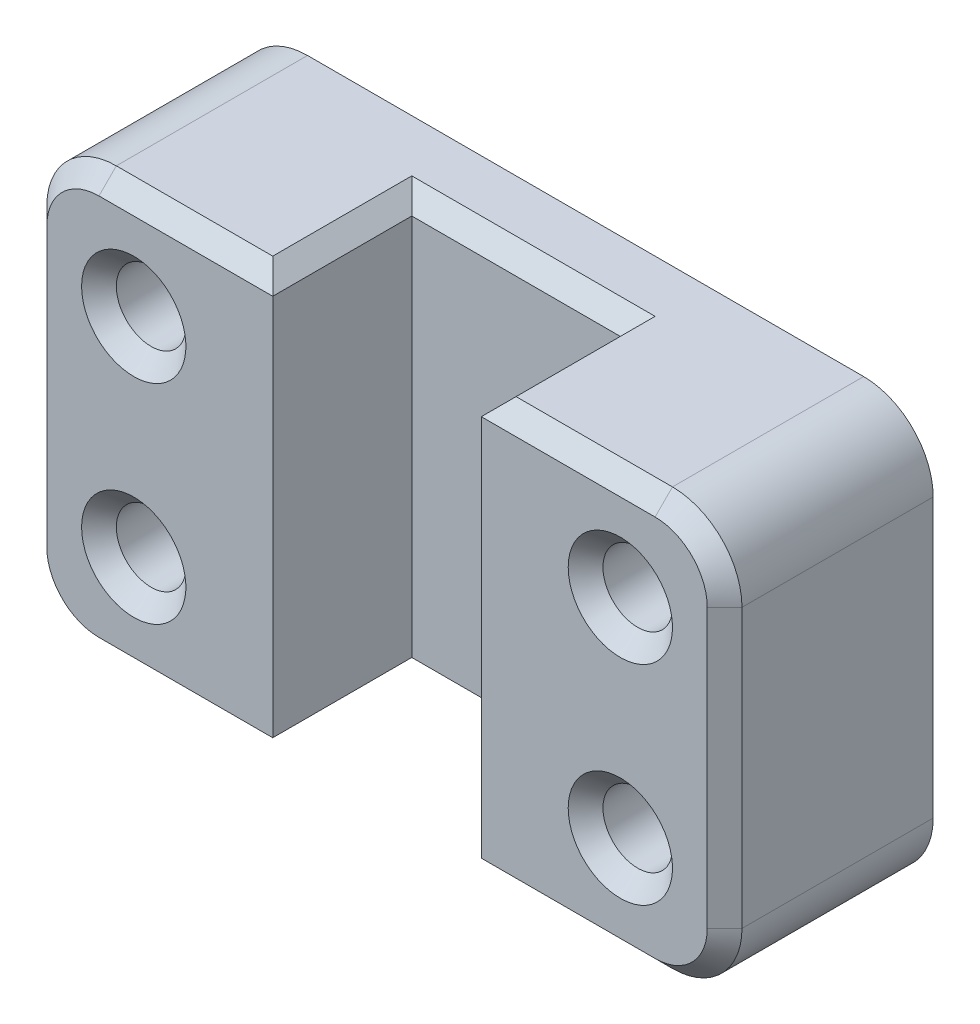
SolidWorks part; units mm, degrees
ref_plane "Front Plane" through (0, 0, 0) normal (0, 0, 1) x (1, 0, 0)
ref_plane "Top Plane" through (0, 0, 0) normal (0, 1, 0) x (1, 0, 0)
ref_plane "Right Plane" through (0, 0, 0) normal (1, 0, 0) x (0, 0, -1)
sketch "Sketch1" plane through (0, 0, 0) normal (0, 0, 1) x (1, 0, 0)
  line L0 (0, 38.1) -> (0, 0) construction
  line L1 (-63.5, -38.1) -> (63.5, -38.1)
  line L2 (-63.5, -38.1) -> (-63.5, 38.1)
  line L3 (-63.5, 38.1) -> (63.5, 38.1)
  line L4 (63.5, -38.1) -> (63.5, 38.1)
  line L5 (-63.5, -38.1) -> (63.5, 38.1) construction
  line L6 (-63.5, 38.1) -> (63.5, -38.1) construction
  line L7 (0, 0) -> (-63.5, 0) construction
  line L8 (0, 38.1) -> (0, 0) construction
  line L9 (0, 0) -> (63.5, 0) construction
  circle A0 centre (-44.45, 19.05) radius 6.35
  circle A1 centre (44.45, 19.05) radius 6.35
  circle A2 centre (-44.45, -19.05) radius 6.35
  circle A3 centre (44.45, -19.05) radius 6.35
  point P0 (0, 0)
  dimension "D3" = 12.7
  dimension "D1" = 76.2
  dimension "D2" = 127
  dimension "D4" = 19.05
  dimension "D5" = 19.05
extrude "Boss-Extrude1" add sketch "Sketch1" along normal blind 38.1
sketch "Sketch3" plane through (0, 0, 38.1) normal (0, 0, 1) x (1, 0, 0)
  line L0 (63.5, 38.1) -> (-63.5, 38.1) construction
  line L1 (-19.05, -38.1) -> (19.05, -38.1)
  line L2 (-19.05, -38.1) -> (-19.05, 38.1)
  line L3 (-19.05, 38.1) -> (19.05, 38.1)
  line L4 (19.05, -38.1) -> (19.05, 38.1)
  line L5 (-19.05, -38.1) -> (19.05, 38.1) construction
  line L6 (-19.05, 38.1) -> (19.05, -38.1) construction
  point P0 (0, 0)
  dimension "D1" = 38.1
extrude "Cut-Extrude1" cut sketch "Sketch3" against normal blind 25.4
fillet "Fillet1" radius 12.7 4 edges at (-63.5, -38.1, 19.05) (63.5, -38.1, 19.05) (63.5, 38.1, 19.05) (-63.5, 38.1, 19.05)
chamfer "Chamfer1" distance 3.175 angle 45 20 edges at (38.1, 19.05, 38.1) (50.8, -19.05, 38.1) (-50.8, -19.05, 38.1) (-38.1, 19.05, 38.1) (19.05, -38.1, 25.4) (0, -38.1, 12.7) (-19.05, -38.1, 25.4) (34.925, -38.1, 38.1) (-34.925, -38.1, 38.1) (59.7803, -34.3803, 38.1) (-59.7803, -34.3803, 38.1) (63.5, 0, 38.1) (-63.5, 0, 38.1) (59.7803, 34.3803, 38.1) (-59.7803, 34.3803, 38.1) (34.925, 38.1, 38.1) (19.05, 38.1, 25.4) (0, 38.1, 12.7) (-19.05, 38.1, 25.4) (-34.925, 38.1, 38.1)
shell "Shell1" thickness 2.54
